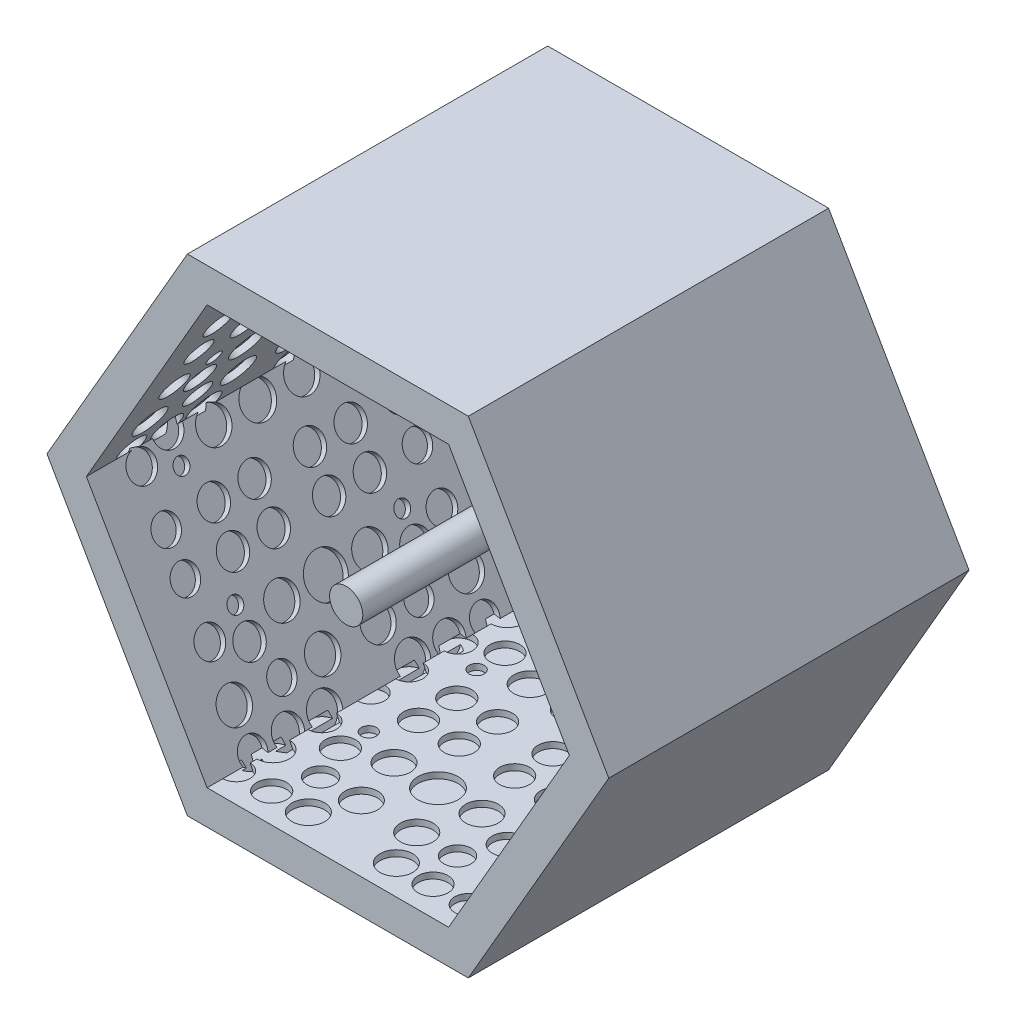
SolidWorks part; units mm, degrees
ref_plane "Alzado" through (0, 0, 0) normal (0, 0, 1) x (1, 0, 0)
ref_plane "Planta" through (0, 0, 0) normal (0, 1, 0) x (1, 0, 0)
ref_plane "Vista lateral" through (0, 0, 0) normal (1, 0, 0) x (0, 0, -1)
sketch "Croquis1" plane through (0, 0, 0) normal (0, 0, 1) x (1, 0, 0)
  line L1 (460, 0) -> (230, 398.3717)
  line L2 (230, 398.3717) -> (-230, 398.3717)
  line L3 (-230, 398.3717) -> (-460, 0)
  line L4 (-460, 0) -> (-230, -398.3717)
  line L5 (-230, -398.3717) -> (230, -398.3717)
  line L6 (230, -398.3717) -> (460, 0)
  circle A0 centre (0, 0) radius 398.3717 construction
extrude "Saliente-Extruir2" add sketch "Croquis1" along normal blind 80
sketch "Croquis3" plane through (0, 0, 80) normal (0, 0, 1) x (1, 0, 0)
  line L1 (395.4525, 0) -> (197.7262, 342.4719)
  line L2 (197.7262, 342.4719) -> (-197.7262, 342.4719)
  line L3 (-197.7262, 342.4719) -> (-395.4525, 0)
  line L4 (-395.4525, 0) -> (-197.7262, -342.4719)
  line L5 (-197.7262, -342.4719) -> (197.7262, -342.4719)
  line L6 (197.7262, -342.4719) -> (395.4525, 0)
  line L7 (460, 0) -> (230, 398.3717)
  line L8 (230, 398.3717) -> (-230, 398.3717)
  line L9 (-230, 398.3717) -> (-460, 0)
  line L10 (-460, 0) -> (-230, -398.3717)
  line L11 (-230, -398.3717) -> (230, -398.3717)
  line L12 (230, -398.3717) -> (460, 0)
  circle A0 centre (0, 0) radius 342.4719 construction
  circle A1 centre (0, 0) radius 398.3717 construction
extrude "Saliente-Extruir5" add sketch "Croquis3" along normal blind 510
sketch "Croquis4" plane through (0, 0, 80) normal (0, 0, 1) x (1, 0, 0)
  circle A0 centre (0, 0) radius 151.6484
extrude "Saliente-Extruir6" add sketch "Croquis4" along normal blind 10
sketch "Croquis5" plane through (0, 342.4719, 0) normal (0, -1, 0) x (1, 0, 0)
  circle A1 centre (-190.0322, 546.7767) radius 22.3728
  circle A3 centre (-132.1516, 546.7767) radius 24.488
  circle A4 centre (-72.0448, 546.7767) radius 26.7141
  circle A5 centre (-45.3307, 486.6699) radius 26.7141
  circle A6 centre (-190.0322, 486.6699) radius 26.7141
  circle A7 centre (-190.0322, 326.3851) radius 22.3728
  circle A8 centre (-112.116, 326.3851) radius 24.488
  circle A9 centre (-45.3307, 326.3851) radius 24.488
  circle A10 centre (-190.0322, 406.5275) radius 23.242
  circle A11 centre (-136.6039, 429.7695) radius 24.488
  circle A12 centre (-112.116, 486.6699) radius 22.2618
  circle A14 centre (-136.6039, 383.2855) radius 12.3769
  circle A15 centre (-72.0448, 406.5275) radius 26.7141
  circle A16 centre (-72.0448, 183.4725) radius 26.7141
  circle A17 centre (-136.6039, 206.7145) radius 12.3769
  circle A18 centre (-112.116, 103.3301) radius 22.2618
  circle A19 centre (-136.6039, 160.2305) radius 24.488
  circle A20 centre (-190.0322, 183.4725) radius 23.242
  circle A21 centre (-45.3307, 263.6149) radius 24.488
  circle A22 centre (-112.116, 263.6149) radius 24.488
  circle A23 centre (-190.0322, 263.6149) radius 22.3728
  circle A24 centre (-190.0322, 103.3301) radius 26.7141
  circle A25 centre (-45.3307, 103.3301) radius 26.7141
  circle A26 centre (-72.0448, 43.2233) radius 26.7141
  circle A27 centre (-132.1516, 43.2233) radius 24.488
  circle A28 centre (-190.0322, 43.2233) radius 22.3728
  circle A29 centre (190.0322, 43.2233) radius 22.3728
  circle A30 centre (132.1516, 43.2233) radius 24.488
  circle A31 centre (72.0448, 43.2233) radius 26.7141
  circle A32 centre (45.3307, 103.3301) radius 26.7141
  circle A33 centre (190.0322, 103.3301) radius 26.7141
  circle A34 centre (190.0322, 263.6149) radius 22.3728
  circle A35 centre (112.116, 263.6149) radius 24.488
  circle A36 centre (45.3307, 263.6149) radius 24.488
  circle A37 centre (190.0322, 183.4725) radius 23.242
  circle A38 centre (136.6039, 160.2305) radius 24.488
  circle A39 centre (112.116, 103.3301) radius 22.2618
  circle A40 centre (136.6039, 206.7145) radius 12.3769
  circle A41 centre (72.0448, 183.4725) radius 26.7141
  circle A42 centre (72.0448, 406.5275) radius 26.7141
  circle A43 centre (136.6039, 383.2855) radius 12.3769
  circle A44 centre (112.116, 486.6699) radius 22.2618
  circle A45 centre (136.6039, 429.7695) radius 24.488
  circle A46 centre (190.0322, 406.5275) radius 23.242
  circle A47 centre (45.3307, 326.3851) radius 24.488
  circle A48 centre (112.116, 326.3851) radius 24.488
  circle A49 centre (190.0322, 326.3851) radius 22.3728
  circle A50 centre (190.0322, 486.6699) radius 26.7141
  circle A51 centre (45.3307, 486.6699) radius 26.7141
  circle A52 centre (72.0448, 546.7767) radius 26.7141
  circle A53 centre (132.1516, 546.7767) radius 24.488
  circle A54 centre (190.0322, 546.7767) radius 22.3728
  circle A55 centre (0, 406.5275) radius 27.7233
  circle A56 centre (0, 183.4725) radius 32.9221
  circle A57 centre (0, 546.7767) radius 27.7233
extrude "Cortar-Extruir1" cut sketch "Croquis5" against normal blind 10
sketch "Croquis7" plane through (296.5894, 171.2359, 0) normal (-0.866, -0.5, 0) x (0, 0, 1)
  circle A0 centre (129.9987, 189.4183) radius 22.3728
  circle A1 centre (187.8793, 189.4183) radius 24.488
  circle A2 centre (247.9861, 189.4183) radius 26.7141
  circle A3 centre (274.7002, 129.3115) radius 26.7141
  circle A4 centre (129.9987, 129.3115) radius 26.7141
  circle A5 centre (129.9987, -30.9732) radius 22.3728
  circle A6 centre (207.9149, -30.9732) radius 24.488
  circle A7 centre (274.7002, -30.9732) radius 24.488
  circle A8 centre (129.9987, 49.1692) radius 23.242
  circle A9 centre (183.4269, 72.4111) radius 24.488
  circle A10 centre (207.9149, 129.3115) radius 22.2618
  circle A11 centre (183.4269, 25.9272) radius 12.3769
  circle A12 centre (247.9861, 49.1692) radius 26.7141
  circle A13 centre (247.9861, -173.8858) radius 26.7141
  circle A14 centre (183.4269, -150.6438) radius 12.3769
  circle A16 centre (183.4269, -197.1278) radius 24.488
  circle A17 centre (129.9987, -173.8858) radius 23.242
  circle A18 centre (274.7002, -93.7434) radius 24.488
  circle A19 centre (207.9149, -93.7434) radius 24.488
  circle A20 centre (129.9987, -93.7434) radius 22.3728
  circle A31 centre (510.0631, -93.7434) radius 22.3728
  circle A32 centre (432.1468, -93.7434) radius 24.488
  circle A33 centre (365.3615, -93.7434) radius 24.488
  circle A34 centre (510.0631, -173.8858) radius 23.242
  circle A35 centre (456.6348, -197.1278) radius 24.488
  circle A37 centre (456.6348, -150.6438) radius 12.3769
  circle A38 centre (392.0756, -173.8858) radius 26.7141
  circle A39 centre (392.0756, 49.1692) radius 26.7141
  circle A40 centre (456.6348, 25.9272) radius 12.3769
  circle A41 centre (432.1468, 129.3115) radius 22.2618
  circle A42 centre (456.6348, 72.4111) radius 24.488
  circle A43 centre (510.0631, 49.1692) radius 23.242
  circle A44 centre (365.3615, -30.9732) radius 24.488
  circle A45 centre (432.1468, -30.9732) radius 24.488
  circle A46 centre (510.0631, -30.9732) radius 22.3728
  circle A47 centre (510.0631, 129.3115) radius 26.7141
  circle A48 centre (365.3615, 129.3115) radius 26.7141
  circle A49 centre (392.0756, 189.4183) radius 26.7141
  circle A50 centre (452.1824, 189.4183) radius 24.488
  circle A51 centre (510.0631, 189.4183) radius 22.3728
  circle A52 centre (320.0309, 49.1692) radius 27.7233
  circle A53 centre (320.0309, -173.8858) radius 32.9221
  circle A54 centre (320.0309, 189.4183) radius 27.7233
extrude "Cortar-Extruir3" cut sketch "Croquis7" against normal blind 10
sketch "Croquis8" plane through (-296.5894, 171.2359, 0) normal (0.866, -0.5, 0) x (0, 0, -1)
  circle A5 centre (-521.3404, 96.5332) radius 22.3728
  circle A6 centre (-443.4242, 96.5332) radius 24.488
  circle A7 centre (-376.6389, 96.5332) radius 24.488
  circle A8 centre (-521.3404, 176.6756) radius 23.242
  circle A9 centre (-467.9122, 199.9176) radius 24.488
  circle A11 centre (-467.9122, 153.4336) radius 12.3769
  circle A12 centre (-403.353, 176.6756) radius 26.7141
  circle A13 centre (-403.353, -46.3794) radius 26.7141
  circle A14 centre (-467.9122, -23.1374) radius 12.3769
  circle A15 centre (-443.4242, -126.5218) radius 22.2618
  circle A16 centre (-467.9122, -69.6213) radius 24.488
  circle A17 centre (-521.3404, -46.3794) radius 23.242
  circle A18 centre (-376.6389, 33.763) radius 24.488
  circle A19 centre (-443.4242, 33.763) radius 24.488
  circle A20 centre (-521.3404, 33.763) radius 22.3728
  circle A21 centre (-521.3404, -126.5218) radius 26.7141
  circle A22 centre (-376.6389, -126.5218) radius 26.7141
  circle A23 centre (-403.353, -186.6285) radius 26.7141
  circle A24 centre (-463.4598, -186.6285) radius 24.488
  circle A25 centre (-521.3404, -186.6285) radius 22.3728
  circle A26 centre (-141.2761, -186.6285) radius 22.3728
  circle A27 centre (-199.1567, -186.6285) radius 24.488
  circle A28 centre (-259.2635, -186.6285) radius 26.7141
  circle A29 centre (-285.9776, -126.5218) radius 26.7141
  circle A30 centre (-141.2761, -126.5218) radius 26.7141
  circle A31 centre (-141.2761, 33.763) radius 22.3728
  circle A32 centre (-219.1923, 33.763) radius 24.488
  circle A33 centre (-285.9776, 33.763) radius 24.488
  circle A34 centre (-141.2761, -46.3794) radius 23.242
  circle A35 centre (-194.7043, -69.6213) radius 24.488
  circle A36 centre (-219.1923, -126.5218) radius 22.2618
  circle A37 centre (-194.7043, -23.1374) radius 12.3769
  circle A38 centre (-259.2635, -46.3794) radius 26.7141
  circle A39 centre (-259.2635, 176.6756) radius 26.7141
  circle A40 centre (-194.7043, 153.4336) radius 12.3769
  circle A42 centre (-194.7043, 199.9176) radius 24.488
  circle A43 centre (-141.2761, 176.6756) radius 23.242
  circle A44 centre (-285.9776, 96.5332) radius 24.488
  circle A45 centre (-219.1923, 96.5332) radius 24.488
  circle A46 centre (-141.2761, 96.5332) radius 22.3728
  circle A52 centre (-331.3083, 176.6756) radius 27.7233
  circle A53 centre (-331.3083, -46.3794) radius 32.9221
extrude "Cortar-Extruir4" cut sketch "Croquis8" against normal blind 10
sketch "Croquis9" plane through (-296.5894, -171.2359, 0) normal (0.866, 0.5, 0) x (0, 0, -1)
  circle A5 centre (-510.6256, 94.9848) radius 22.3728
  circle A6 centre (-432.7093, 94.9848) radius 24.488
  circle A7 centre (-365.924, 94.9848) radius 24.488
  circle A8 centre (-510.6256, 175.1272) radius 23.242
  circle A9 centre (-457.1973, 198.3692) radius 24.488
  circle A11 centre (-457.1973, 151.8852) radius 12.3769
  circle A12 centre (-392.6381, 175.1272) radius 26.7141
  circle A13 centre (-392.6381, -47.9278) radius 26.7141
  circle A14 centre (-457.1973, -24.6858) radius 12.3769
  circle A15 centre (-432.7093, -128.0702) radius 22.2618
  circle A16 centre (-457.1973, -71.1697) radius 24.488
  circle A17 centre (-510.6256, -47.9278) radius 23.242
  circle A18 centre (-365.924, 32.2146) radius 24.488
  circle A19 centre (-432.7093, 32.2146) radius 24.488
  circle A20 centre (-510.6256, 32.2146) radius 22.3728
  circle A21 centre (-510.6256, -128.0702) radius 26.7141
  circle A22 centre (-365.924, -128.0702) radius 26.7141
  circle A23 centre (-392.6381, -188.1769) radius 26.7141
  circle A24 centre (-452.7449, -188.1769) radius 24.488
  circle A25 centre (-510.6256, -188.1769) radius 22.3728
  circle A26 centre (-130.5612, -188.1769) radius 22.3728
  circle A27 centre (-188.4418, -188.1769) radius 24.488
  circle A28 centre (-248.5486, -188.1769) radius 26.7141
  circle A29 centre (-275.2627, -128.0702) radius 26.7141
  circle A30 centre (-130.5612, -128.0702) radius 26.7141
  circle A31 centre (-130.5612, 32.2146) radius 22.3728
  circle A32 centre (-208.4774, 32.2146) radius 24.488
  circle A33 centre (-275.2627, 32.2146) radius 24.488
  circle A34 centre (-130.5612, -47.9278) radius 23.242
  circle A35 centre (-183.9894, -71.1697) radius 24.488
  circle A36 centre (-208.4774, -128.0702) radius 22.2618
  circle A37 centre (-183.9894, -24.6858) radius 12.3769
  circle A38 centre (-248.5486, -47.9278) radius 26.7141
  circle A39 centre (-248.5486, 175.1272) radius 26.7141
  circle A40 centre (-183.9894, 151.8852) radius 12.3769
  circle A42 centre (-183.9894, 198.3692) radius 24.488
  circle A43 centre (-130.5612, 175.1272) radius 23.242
  circle A44 centre (-275.2627, 94.9848) radius 24.488
  circle A45 centre (-208.4774, 94.9848) radius 24.488
  circle A46 centre (-130.5612, 94.9848) radius 22.3728
  circle A52 centre (-320.5934, 175.1272) radius 27.7233
  circle A53 centre (-320.5934, -47.9278) radius 32.9221
extrude "Cortar-Extruir5" cut sketch "Croquis9" against normal blind 10
sketch "Croquis10" plane through (0, -342.4719, 0) normal (0, 1, 0) x (1, 0, 0)
  circle A0 centre (-198.1204, -38.2313) radius 22.3728
  circle A1 centre (-140.2398, -38.2313) radius 24.488
  circle A2 centre (-80.133, -38.2313) radius 26.7141
  circle A3 centre (-53.4189, -98.3381) radius 26.7141
  circle A4 centre (-198.1204, -98.3381) radius 26.7141
  circle A5 centre (-198.1204, -258.6229) radius 22.3728
  circle A6 centre (-120.2042, -258.6229) radius 24.488
  circle A7 centre (-53.4189, -258.6229) radius 24.488
  circle A8 centre (-198.1204, -178.4805) radius 23.242
  circle A9 centre (-144.6922, -155.2385) radius 24.488
  circle A10 centre (-120.2042, -98.3381) radius 22.2618
  circle A11 centre (-144.6922, -201.7225) radius 12.3769
  circle A12 centre (-80.133, -178.4805) radius 26.7141
  circle A13 centre (-80.133, -401.5355) radius 26.7141
  circle A14 centre (-144.6922, -378.2935) radius 12.3769
  circle A15 centre (-120.2042, -481.6779) radius 22.2618
  circle A16 centre (-144.6922, -424.7775) radius 24.488
  circle A17 centre (-198.1204, -401.5355) radius 23.242
  circle A18 centre (-53.4189, -321.3931) radius 24.488
  circle A19 centre (-120.2042, -321.3931) radius 24.488
  circle A20 centre (-198.1204, -321.3931) radius 22.3728
  circle A21 centre (-198.1204, -481.6779) radius 26.7141
  circle A22 centre (-53.4189, -481.6779) radius 26.7141
  circle A23 centre (-80.133, -541.7847) radius 26.7141
  circle A24 centre (-140.2398, -541.7847) radius 24.488
  circle A25 centre (-198.1204, -541.7847) radius 22.3728
  circle A26 centre (181.9439, -541.7847) radius 22.3728
  circle A27 centre (124.0633, -541.7847) radius 24.488
  circle A28 centre (63.9565, -541.7847) radius 26.7141
  circle A29 centre (37.2424, -481.6779) radius 26.7141
  circle A30 centre (181.9439, -481.6779) radius 26.7141
  circle A31 centre (181.9439, -321.3931) radius 22.3728
  circle A32 centre (104.0277, -321.3931) radius 24.488
  circle A33 centre (37.2424, -321.3931) radius 24.488
  circle A34 centre (181.9439, -401.5355) radius 23.242
  circle A35 centre (128.5157, -424.7775) radius 24.488
  circle A36 centre (104.0277, -481.6779) radius 22.2618
  circle A37 centre (128.5157, -378.2935) radius 12.3769
  circle A38 centre (63.9565, -401.5355) radius 26.7141
  circle A39 centre (63.9565, -178.4805) radius 26.7141
  circle A40 centre (128.5157, -201.7225) radius 12.3769
  circle A41 centre (104.0277, -98.3381) radius 22.2618
  circle A42 centre (128.5157, -155.2385) radius 24.488
  circle A43 centre (181.9439, -178.4805) radius 23.242
  circle A44 centre (37.2424, -258.6229) radius 24.488
  circle A45 centre (104.0277, -258.6229) radius 24.488
  circle A46 centre (181.9439, -258.6229) radius 22.3728
  circle A47 centre (181.9439, -98.3381) radius 26.7141
  circle A48 centre (37.2424, -98.3381) radius 26.7141
  circle A49 centre (63.9565, -38.2313) radius 26.7141
  circle A50 centre (124.0633, -38.2313) radius 24.488
  circle A51 centre (181.9439, -38.2313) radius 22.3728
  circle A52 centre (-8.0883, -178.4805) radius 27.7233
  circle A53 centre (-8.0883, -401.5355) radius 32.9221
  circle A54 centre (-8.0883, -38.2313) radius 27.7233
extrude "Cortar-Extruir6" cut sketch "Croquis10" against normal blind 10
sketch "Croquis11" plane through (296.5894, -171.2359, 0) normal (-0.866, 0.5, 0) x (0, 0, 1)
  circle A0 centre (131.7998, 182.3592) radius 22.3728
  circle A1 centre (189.6804, 182.3592) radius 24.488
  circle A2 centre (249.7872, 182.3592) radius 26.7141
  circle A3 centre (276.5014, 122.2524) radius 26.7141
  circle A4 centre (131.7998, 122.2524) radius 26.7141
  circle A5 centre (131.7998, -38.0324) radius 22.3728
  circle A6 centre (209.716, -38.0324) radius 24.488
  circle A7 centre (276.5014, -38.0324) radius 24.488
  circle A8 centre (131.7998, 42.11) radius 23.242
  circle A9 centre (185.2281, 65.352) radius 24.488
  circle A10 centre (209.716, 122.2524) radius 22.2618
  circle A11 centre (185.2281, 18.868) radius 12.3769
  circle A12 centre (249.7872, 42.11) radius 26.7141
  circle A13 centre (249.7872, -180.945) radius 26.7141
  circle A14 centre (185.2281, -157.703) radius 12.3769
  circle A16 centre (185.2281, -204.1869) radius 24.488
  circle A17 centre (131.7998, -180.945) radius 23.242
  circle A18 centre (276.5014, -100.8026) radius 24.488
  circle A19 centre (209.716, -100.8026) radius 24.488
  circle A20 centre (131.7998, -100.8026) radius 22.3728
  circle A31 centre (511.8642, -100.8026) radius 22.3728
  circle A32 centre (433.948, -100.8026) radius 24.488
  circle A33 centre (367.1627, -100.8026) radius 24.488
  circle A34 centre (511.8642, -180.945) radius 23.242
  circle A35 centre (458.4359, -204.1869) radius 24.488
  circle A37 centre (458.4359, -157.703) radius 12.3769
  circle A38 centre (393.8768, -180.945) radius 26.7141
  circle A39 centre (393.8768, 42.11) radius 26.7141
  circle A40 centre (458.4359, 18.868) radius 12.3769
  circle A41 centre (433.948, 122.2524) radius 22.2618
  circle A42 centre (458.4359, 65.352) radius 24.488
  circle A43 centre (511.8642, 42.11) radius 23.242
  circle A44 centre (367.1627, -38.0324) radius 24.488
  circle A45 centre (433.948, -38.0324) radius 24.488
  circle A46 centre (511.8642, -38.0324) radius 22.3728
  circle A47 centre (511.8642, 122.2524) radius 26.7141
  circle A48 centre (367.1627, 122.2524) radius 26.7141
  circle A49 centre (393.8768, 182.3592) radius 26.7141
  circle A50 centre (453.9836, 182.3592) radius 24.488
  circle A51 centre (511.8642, 182.3592) radius 22.3728
  circle A52 centre (321.832, 42.11) radius 27.7233
  circle A53 centre (321.832, -180.945) radius 32.9221
  circle A54 centre (321.832, 182.3592) radius 27.7233
extrude "Cortar-Extruir7" cut sketch "Croquis11" against normal blind 10
sketch "Croquis12" plane through (0, 0, 90) normal (0, 0, 1) x (1, 0, 0)
  circle A0 centre (0, 0) radius 27.2238
extrude "Saliente-Extruir7" add sketch "Croquis12" along normal blind 470
sketch "Croquis13" plane through (0, 0, 0) normal (0, 0, -1) x (-1, 0, 0)
  circle A0 centre (0, 0) radius 241.4978
extrude "Saliente-Extruir8" add sketch "Croquis13" along normal blind 20
